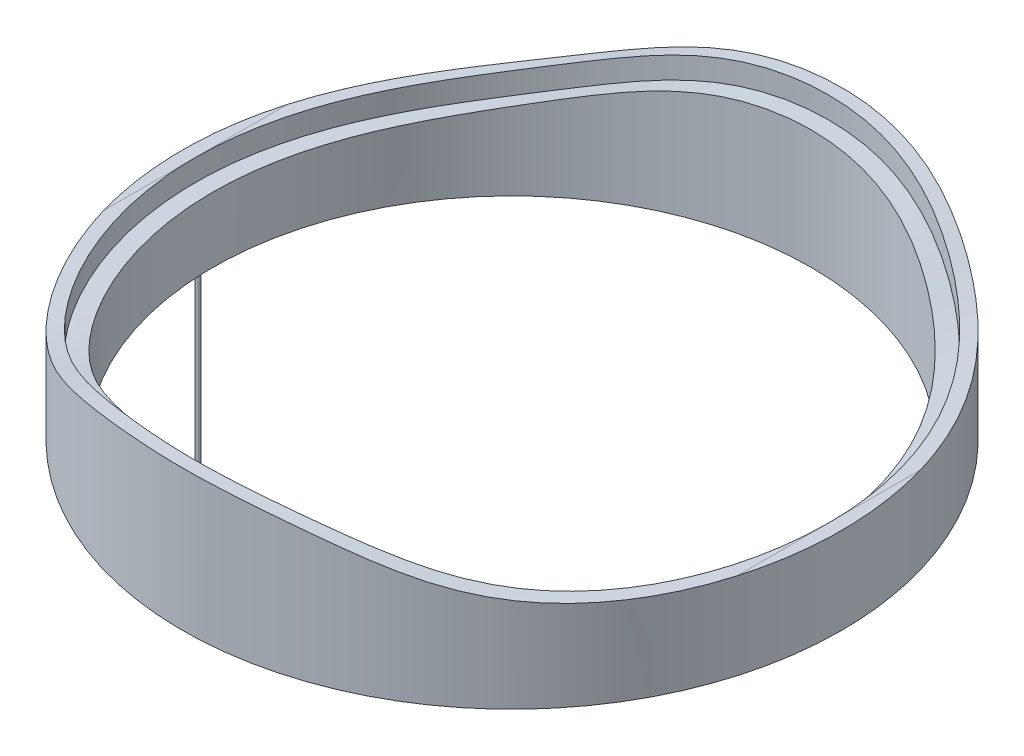
SolidWorks part; units mm, degrees
ref_plane "Ebene vorne" through (0, 0, 0) normal (0, 0, 1) x (1, 0, 0)
ref_plane "Ebene oben" through (0, 0, 0) normal (0, 1, 0) x (1, 0, 0)
ref_plane "Ebene rechts" through (0, 0, 0) normal (1, 0, 0) x (0, 0, -1)
sketch "Sketch1" plane through (0, 0, 0) normal (0, 1, 0) x (1, 0, 0)
  circle A0 centre (0, 0) radius 73.1
  dimension "D1" = 146.2
extrude "Extrude-Thin1" add sketch "Sketch1" along normal blind 30 thin thin type one direction reverse wall 4
sketch "Sketch2" plane through (0, 0, 0) normal (0, 0, 1) x (1, 0, 0)
  line L2 (-73.1, 15) -> (73.1, 15)
  line L5 (95.9858, 15) -> (47.9858, 15) construction
  line L6 (-49.714, 15) -> (-97.714, 15) construction
  line L7 (28.7889, 27.5) -> (-28.8558, 27.5) construction
  line L8 (-73.1, 15) -> (-73.1, 30)
  line L9 (-73.1, 30) -> (0, 30)
  line L10 (69.1, 30) -> (-69.1, 30) construction
  line L11 (0, 30) -> (73.1, 30)
  line L12 (73.1, 30) -> (73.1, 15)
  line L13 (-73.1, 10) -> (73.1, 10) construction
  line L16 (-73.1, 0) -> (73.1, 0) construction
  spline S0 degree 3 poles (-73.1, 15) (-43.1, 15) (-36.0233, 27.6042) (36.0233, 27.6042) (43.1, 15) (73.1, 15) knots 0 0 0 0 0.45 0.55 1 1 1 1
  dimension "D2" = 200
  dimension "D3" = 100
  dimension "D4" = 12.5
  dimension "D1" = 100
  dimension "D5" = 5
  dimension "D6" = 10
extrude "Cut-Extrude1" cut sketch "Sketch2" against normal mid plane 150 contours L8 S0 L12 L11 L9
sketch "Sketch3" plane through (0, 0, 0) normal (0, 1, 0) x (1, 0, 0)
  circle A0 centre (0, 0) radius 73.1
extrude "Extrude-Thin2" add sketch "Sketch3" along normal blind 50 thin
sketch "Sketch4" plane through (0, 0, 0) normal (0, 0, 1) x (1, 0, 0)
  line L0 (-76.1, 25) -> (76.1, 25) construction
  line L1 (-76.1, 50) -> (-76.1, 0) construction
  line L2 (76.1, 0) -> (76.1, 50) construction
  line L3 (-73.1, 20) -> (73.1, 20)
  line L4 (-73.1, 15) -> (-73.1, 30) construction
  line L5 (73.1, 30) -> (73.1, 15) construction
  line L6 (-73.1, 15) -> (73.1, 15) construction
  line L7 (26.5151, 32.5) -> (-26.8549, 32.5) construction
  line L8 (-49.9895, 20) -> (-97.9895, 20) construction
  line L9 (95.1062, 20) -> (47.1062, 20) construction
  line L10 (-73.1, 20) -> (-76.1, 20)
  line L11 (-76.1, 20) -> (-76.1, 50)
  line L12 (-76.1, 50) -> (76.1, 50)
  line L13 (76.1, 50) -> (76.1, 20)
  line L14 (76.1, 20) -> (73.1, 20)
  spline S0 degree 3 poles (-73.1, 20) (-43.1, 20) (-36.0233, 32.6042) (36.0233, 32.6042) (43.1, 20) (73.1, 20) knots 0 0 0 0 0.45 0.55 1 1 1 1
  dimension "D2" = 200
  dimension "D3" = 100
  dimension "D4" = 100
  dimension "D1" = 5
  dimension "D5" = 12.5
extrude "Cut-Extrude2" cut sketch "Sketch4" against normal mid plane 155 contours L10 S0 L14 L13 L12 L11
sketch "Sketch5" plane through (0, 0, 0) normal (0, -1, 0) x (1, 0, 0)
  line L0 (90.9706, 0) -> (-115.9709, 0) construction
  circle A0 centre (-72.5, 0) radius 0.5
  point P14 (0, 0)
  dimension "D1" = 1
  dimension "D2" = 72.5
extrude "Boss-Extrude1" add sketch "Sketch5" along normal blind 50
